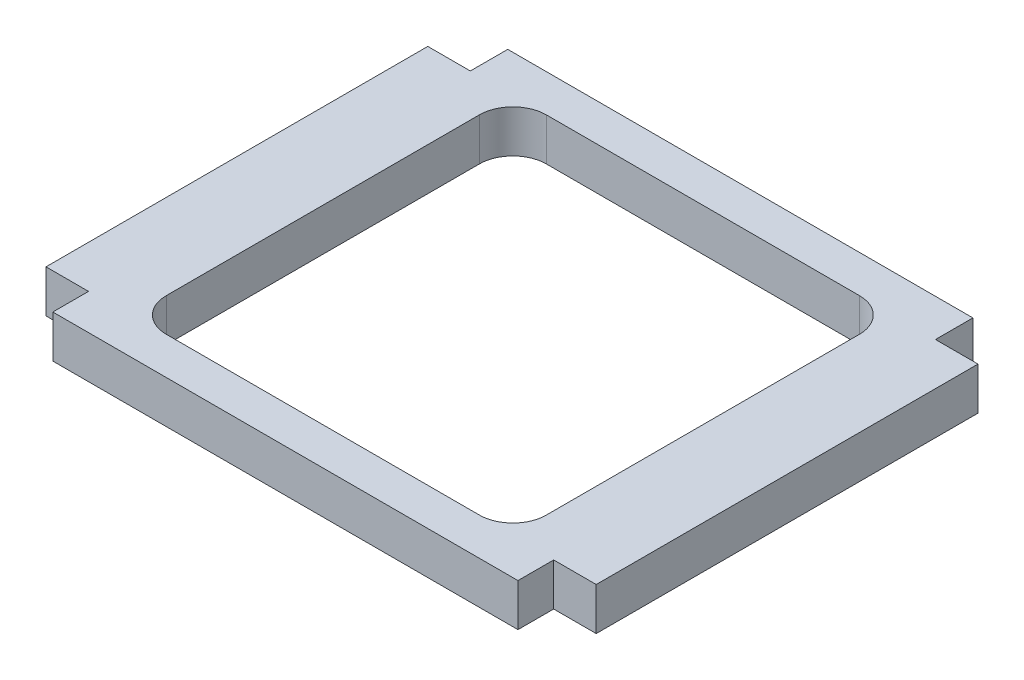
SolidWorks part; units mm, degrees
ref_plane "Front Plane" through (0, 0, 0) normal (0, 0, 1) x (1, 0, 0)
ref_plane "Top Plane" through (0, 0, 0) normal (0, 1, 0) x (1, 0, 0)
ref_plane "Right Plane" through (0, 0, 0) normal (1, 0, 0) x (0, 0, -1)
sketch "Sketch1" plane through (0, 0, 0) normal (0, 1, 0) x (1, 0, 0)
  line L0 (-41.0718, -28.6282) -> (-41.0718, 28.3718)
  line L1 (-23.3718, -28.3718) -> (23.3718, -28.3718)
  line L2 (-28.3718, -23.3718) -> (-28.3718, 23.3718)
  line L3 (-23.3718, 28.3718) -> (23.3718, 28.3718)
  line L4 (28.3718, -23.3718) -> (28.3718, 23.3718)
  line L5 (-28.3718, -28.3718) -> (28.3718, 28.3718) construction
  line L6 (-28.3718, 28.3718) -> (28.3718, -28.3718) construction
  line L7 (-41.0718, 28.3718) -> (-34.7218, 28.3718)
  line L8 (41.0718, -28.6282) -> (41.0718, 28.3718)
  line L9 (28.3718, -28.3718) -> (28.3718, 28.3718) construction
  line L10 (-34.7218, -33.9598) -> (34.7218, -33.9598)
  line L11 (-41.0718, -41.0718) -> (-41.0718, 41.0718) construction
  line L12 (-41.0718, -41.0718) -> (41.0718, -41.0718) construction
  line L13 (41.0718, -41.0718) -> (41.0718, 41.0718) construction
  line L14 (-28.3718, 28.3718) -> (28.3718, 28.3718) construction
  line L15 (-28.3718, -28.3718) -> (28.3718, -28.3718) construction
  line L16 (-28.3718, -28.3718) -> (-28.3718, 28.3718) construction
  line L17 (-41.0718, -28.6282) -> (-34.7218, -28.6282)
  line L18 (-34.7218, -33.9598) -> (-34.7218, -28.6282)
  line L19 (-34.7218, 33.9598) -> (34.7218, 33.9598)
  line L20 (-34.7218, 28.3718) -> (-34.7218, 33.9598)
  line L21 (41.0718, -28.6282) -> (34.7218, -28.6282)
  line L22 (34.7218, -33.9598) -> (34.7218, -28.6282)
  line L23 (-41.0718, 41.0718) -> (41.0718, 41.0718) construction
  line L24 (34.7218, 28.3718) -> (34.7218, 33.9598)
  line L25 (34.7218, 28.3718) -> (41.0718, 28.3718)
  arc A0 (28.3718, 23.3718) -> (23.3718, 28.3718) centre (23.3718, 23.3718) ccw
  arc A1 (28.3718, -23.3718) -> (23.3718, -28.3718) centre (23.3718, -23.3718) cw
  arc A2 (-23.3718, -28.3718) -> (-28.3718, -23.3718) centre (-23.3718, -23.3718) cw
  arc A3 (-28.3718, 23.3718) -> (-23.3718, 28.3718) centre (-23.3718, 23.3718) cw
  point P0 (0, 0)
  dimension "D7" = 5
  dimension "D1" = 56.7436
  dimension "D2" = 56.7436
  dimension "D4" = 5.588
  dimension "D5" = 6.35
  dimension "D6" = 6.35
  dimension "D8" = 5.588
  dimension "D3" = 12.7
extrude "Boss-Extrude1" add sketch "Sketch1" along normal blind 6.35
